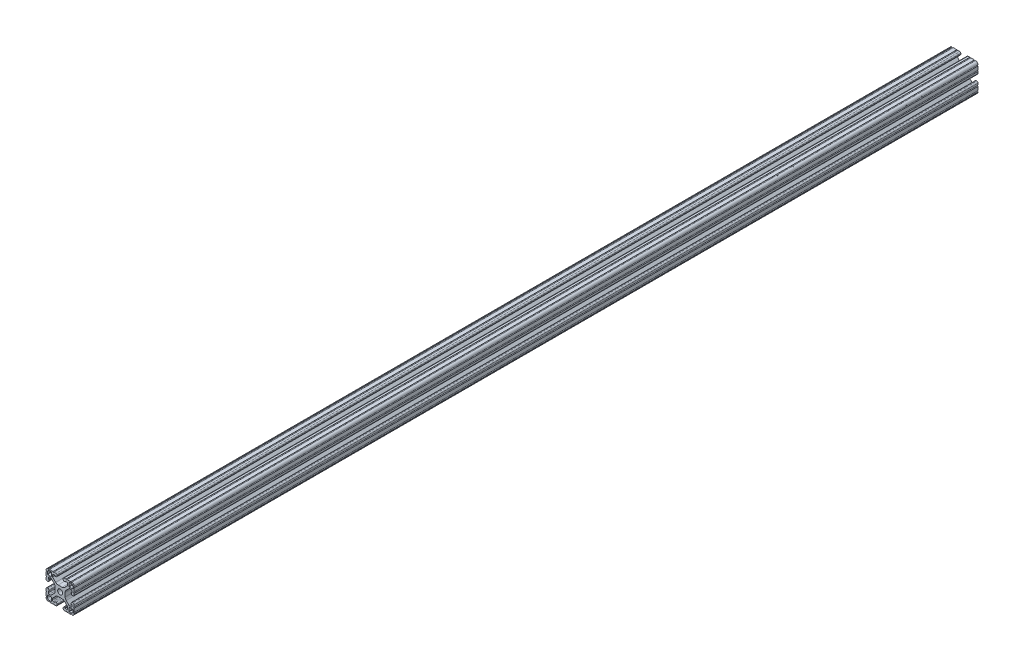
SolidWorks part; units mm, degrees
material "6061 Alloy"
ref_plane "Front Plane" through (0, 0, 0) normal (0, 0, 1) x (1, 0, 0)
ref_plane "Top Plane" through (0, 0, 0) normal (0, 1, 0) x (1, 0, 0)
ref_plane "Right Plane" through (0, 0, 0) normal (1, 0, 0) x (0, 0, -1)
sketch "Sketch1" plane through (0, 0, 0) normal (0, 0, 1) x (1, 0, 0)
  line L0 (0, 21.507) -> (0, -20.9529) construction
  line L1 (20.4424, 0) -> (-20.8151, 0) construction
  line L2 (10.0267, -12.1519) -> (6.0215, -8.1473)
  line L3 (-10.0267, 12.1519) -> (-6.0215, 8.1473)
  line L4 (-10.287, 14.5547) -> (-10.287, 12.7802)
  line L5 (-6.8141, 15.8247) -> (-9.017, 15.8247)
  line L6 (10.287, -14.5547) -> (10.287, -12.7802)
  line L7 (-6.8141, 14.986) -> (-6.8141, 15.8247)
  line L8 (6.8141, -15.8247) -> (9.017, -15.8247)
  line L9 (-2.6631, -6.7564) -> (2.6631, -6.7564)
  line L10 (6.8141, -14.986) -> (6.8141, -15.8247)
  line L11 (5.6388, -14.986) -> (6.8141, -14.986)
  line L12 (4.064, -17.4752) -> (4.064, -16.5608)
  line L13 (7.9756, -19.05) -> (5.6388, -19.05)
  line L14 (14.3256, -19.05) -> (9.4996, -19.05)
  line L15 (15.875, -19.05) -> (15.8496, -19.05)
  line L16 (19.05, -15.8496) -> (19.05, -15.875)
  line L17 (19.05, -9.4996) -> (19.05, -14.3256)
  line L18 (19.05, -5.6388) -> (19.05, -7.9756)
  line L19 (-5.6388, 14.986) -> (-6.8141, 14.986)
  line L20 (-4.064, 17.4752) -> (-4.064, 16.5608)
  line L21 (-7.9756, 19.05) -> (-5.6388, 19.05)
  line L22 (16.5608, -4.064) -> (17.4752, -4.064)
  line L23 (-14.3256, 19.05) -> (-9.4996, 19.05)
  line L24 (14.986, -6.7506) -> (14.986, -5.6388)
  line L25 (15.879, -6.7506) -> (14.986, -6.7506)
  line L26 (-15.875, 19.05) -> (-15.8496, 19.05)
  line L27 (-19.05, 15.8496) -> (-19.05, 15.875)
  line L28 (15.879, -8.9192) -> (15.879, -6.7506)
  line L29 (12.7428, -10.1892) -> (14.609, -10.1892)
  line L30 (-19.05, 9.4996) -> (-19.05, 14.3256)
  line L31 (-19.05, 5.6388) -> (-19.05, 7.9756)
  line L32 (8.1479, -5.9632) -> (12.1142, -9.9289)
  line L33 (16.891, -11.8618) -> (12.2428, -11.8618)
  line L34 (11.8618, -12.2428) -> (11.8618, -16.891)
  line L35 (12.2428, -17.272) -> (14.478, -17.272)
  line L36 (17.272, 14.478) -> (17.272, 12.2428)
  line L37 (12.2428, 17.272) -> (14.478, 17.272)
  line L38 (11.8618, 12.2428) -> (11.8618, 16.891)
  line L39 (16.891, 11.8618) -> (12.2428, 11.8618)
  line L40 (17.272, -14.478) -> (17.272, -12.2428)
  line L41 (-16.5608, 4.064) -> (-17.4752, 4.064)
  line L42 (-14.986, 6.7506) -> (-14.986, 5.6388)
  line L43 (-15.879, 6.7506) -> (-14.986, 6.7506)
  line L44 (-15.879, 8.9192) -> (-15.879, 6.7506)
  line L45 (-12.7428, 10.1892) -> (-14.609, 10.1892)
  line L46 (-8.1479, 5.9632) -> (-12.1142, 9.9289)
  line L47 (-6.7564, -2.6043) -> (-6.7564, 2.6043)
  line L48 (-17.272, -14.478) -> (-17.272, -12.2428)
  line L49 (-16.891, 11.8618) -> (-12.2428, 11.8618)
  line L50 (-11.8618, 12.2428) -> (-11.8618, 16.891)
  line L51 (-12.2428, 17.272) -> (-14.478, 17.272)
  line L52 (-17.272, 14.478) -> (-17.272, 12.2428)
  line L53 (-12.2428, -17.272) -> (-14.478, -17.272)
  line L54 (-11.8618, -12.2428) -> (-11.8618, -16.891)
  line L55 (-16.891, -11.8618) -> (-12.2428, -11.8618)
  line L56 (-8.1479, -5.9632) -> (-12.1142, -9.9289)
  line L57 (-12.7428, -10.1892) -> (-14.609, -10.1892)
  line L58 (-15.879, -8.9192) -> (-15.879, -6.7506)
  line L59 (-15.879, -6.7506) -> (-14.986, -6.7506)
  line L60 (-14.986, -6.7506) -> (-14.986, -5.6388)
  line L61 (-16.5608, -4.064) -> (-17.4752, -4.064)
  line L62 (-19.05, -5.6388) -> (-19.05, -7.9756)
  line L63 (-19.05, -9.4996) -> (-19.05, -14.3256)
  line L64 (-19.05, -15.8496) -> (-19.05, -15.875)
  line L65 (-15.875, -19.05) -> (-15.8496, -19.05)
  line L66 (-14.3256, -19.05) -> (-9.4996, -19.05)
  line L67 (-7.9756, -19.05) -> (-5.6388, -19.05)
  line L68 (-4.064, -17.4752) -> (-4.064, -16.5608)
  line L69 (-5.6388, -14.986) -> (-6.8141, -14.986)
  line L70 (-6.8141, -14.986) -> (-6.8141, -15.8247)
  line L71 (-6.8141, -15.8247) -> (-9.017, -15.8247)
  line L72 (-10.287, -14.5547) -> (-10.287, -12.7802)
  line L73 (-10.0267, -12.1519) -> (-6.0215, -8.1473)
  line L95 (6.7564, -2.6043) -> (6.7564, 2.6043)
  line L96 (8.1479, 5.9632) -> (12.1142, 9.9289)
  line L97 (12.7428, 10.1892) -> (14.609, 10.1892)
  line L98 (15.879, 8.9192) -> (15.879, 6.7506)
  line L99 (15.879, 6.7506) -> (14.986, 6.7506)
  line L100 (14.986, 6.7506) -> (14.986, 5.6388)
  line L101 (16.5608, 4.064) -> (17.4752, 4.064)
  line L102 (19.05, 5.6388) -> (19.05, 7.9756)
  line L103 (19.05, 9.4996) -> (19.05, 14.3256)
  line L104 (19.05, 15.8496) -> (19.05, 15.875)
  line L105 (15.875, 19.05) -> (15.8496, 19.05)
  line L106 (14.3256, 19.05) -> (9.4996, 19.05)
  line L107 (7.9756, 19.05) -> (5.6388, 19.05)
  line L108 (4.064, 17.4752) -> (4.064, 16.5608)
  line L109 (5.6388, 14.986) -> (6.8141, 14.986)
  line L110 (6.8141, 14.986) -> (6.8141, 15.8247)
  line L111 (6.8141, 15.8247) -> (9.017, 15.8247)
  line L112 (10.287, 14.5547) -> (10.287, 12.7802)
  line L113 (10.0267, 12.1519) -> (6.0215, 8.1473)
  line L114 (2.6631, 6.7564) -> (-2.6631, 6.7564)
  arc A0 (10.0267, -12.1519) -> (10.287, -12.7802) centre (9.3985, -12.7802) cw
  arc A1 (10.287, -14.5547) -> (9.017, -15.8247) centre (9.017, -14.5547) cw
  arc A2 (4.064, -16.5608) -> (5.6388, -14.986) centre (5.6388, -16.5608) cw
  arc A3 (-10.0267, 12.1519) -> (-10.287, 12.7802) centre (-9.3985, 12.7802) cw
  arc A4 (-10.287, 14.5547) -> (-9.017, 15.8247) centre (-9.017, 14.5547) cw
  arc A5 (5.6388, -19.05) -> (4.064, -17.4752) centre (5.6388, -17.4752) cw
  arc A6 (7.9756, -19.05) -> (9.4996, -19.05) centre (8.7376, -19.05) cw
  arc A7 (-4.064, 16.5608) -> (-5.6388, 14.986) centre (-5.6388, 16.5608) cw
  arc A8 (14.3256, -19.05) -> (15.8496, -19.05) centre (15.0876, -19.05) cw
  arc A9 (19.05, -15.875) -> (15.875, -19.05) centre (15.875, -15.875) cw
  arc A10 (6.0215, -8.1473) -> (2.6631, -6.7564) centre (2.6631, -11.5062) ccw
  arc A11 (-6.0215, -8.1473) -> (-2.6631, -6.7564) centre (-2.6631, -11.5062) cw
  arc A12 (19.05, -15.8496) -> (19.05, -14.3256) centre (19.05, -15.0876) cw
  arc A13 (19.05, -9.4996) -> (19.05, -7.9756) centre (19.05, -8.7376) cw
  arc A14 (17.4752, -4.064) -> (19.05, -5.6388) centre (17.4752, -5.6388) cw
  arc A15 (14.986, -5.6388) -> (16.5608, -4.064) centre (16.5608, -5.6388) cw
  arc A16 (15.879, -8.9192) -> (14.609, -10.1892) centre (14.609, -8.9192) cw
  arc A17 (12.7428, -10.1892) -> (12.1142, -9.9289) centre (12.7428, -9.3002) cw
  arc A18 (16.891, -11.8618) -> (17.272, -12.2428) centre (16.891, -12.2428) cw
  arc A19 (-5.6388, 19.05) -> (-4.064, 17.4752) centre (-5.6388, 17.4752) cw
  arc A20 (-7.9756, 19.05) -> (-9.4996, 19.05) centre (-8.7376, 19.05) cw
  arc A21 (-14.3256, 19.05) -> (-15.8496, 19.05) centre (-15.0876, 19.05) cw
  arc A22 (11.8618, -12.2428) -> (12.2428, -11.8618) centre (12.2428, -12.2428) cw
  arc A23 (-19.05, 15.875) -> (-15.875, 19.05) centre (-15.875, 15.875) cw
  arc A24 (12.2428, -17.272) -> (11.8618, -16.891) centre (12.2428, -16.891) cw
  arc A25 (17.272, -14.478) -> (14.478, -17.272) centre (14.478, -14.478) cw
  arc A26 (-19.05, 15.8496) -> (-19.05, 14.3256) centre (-19.05, 15.0876) cw
  arc A27 (-19.05, 9.4996) -> (-19.05, 7.9756) centre (-19.05, 8.7376) cw
  arc A28 (-17.4752, 4.064) -> (-19.05, 5.6388) centre (-17.4752, 5.6388) cw
  arc A29 (-14.986, 5.6388) -> (-16.5608, 4.064) centre (-16.5608, 5.6388) cw
  arc A30 (-15.879, 8.9192) -> (-14.609, 10.1892) centre (-14.609, 8.9192) cw
  arc A31 (-12.7428, 10.1892) -> (-12.1142, 9.9289) centre (-12.7428, 9.3002) cw
  arc A32 (-8.1479, 5.9632) -> (-6.7564, 2.6043) centre (-11.5062, 2.6043) cw
  arc A33 (-6.7564, -2.6043) -> (-8.1479, -5.9632) centre (-11.5062, -2.6043) cw
  arc A34 (-16.891, 11.8618) -> (-17.272, 12.2428) centre (-16.891, 12.2428) cw
  arc A35 (-11.8618, 12.2428) -> (-12.2428, 11.8618) centre (-12.2428, 12.2428) cw
  arc A36 (17.272, 14.478) -> (14.478, 17.272) centre (14.478, 14.478) ccw
  arc A37 (12.2428, 17.272) -> (11.8618, 16.891) centre (12.2428, 16.891) ccw
  arc A38 (11.8618, 12.2428) -> (12.2428, 11.8618) centre (12.2428, 12.2428) ccw
  arc A39 (16.891, 11.8618) -> (17.272, 12.2428) centre (16.891, 12.2428) ccw
  arc A40 (-12.2428, 17.272) -> (-11.8618, 16.891) centre (-12.2428, 16.891) cw
  circle A41 centre (0, 0) radius 3.3274
  arc A42 (-17.272, 14.478) -> (-14.478, 17.272) centre (-14.478, 14.478) cw
  arc A43 (-17.272, -14.478) -> (-14.478, -17.272) centre (-14.478, -14.478) ccw
  arc A44 (-12.2428, -17.272) -> (-11.8618, -16.891) centre (-12.2428, -16.891) ccw
  arc A45 (-11.8618, -12.2428) -> (-12.2428, -11.8618) centre (-12.2428, -12.2428) ccw
  arc A46 (-16.891, -11.8618) -> (-17.272, -12.2428) centre (-16.891, -12.2428) ccw
  arc A47 (-12.7428, -10.1892) -> (-12.1142, -9.9289) centre (-12.7428, -9.3002) ccw
  arc A48 (-15.879, -8.9192) -> (-14.609, -10.1892) centre (-14.609, -8.9192) ccw
  arc A49 (-14.986, -5.6388) -> (-16.5608, -4.064) centre (-16.5608, -5.6388) ccw
  arc A50 (-17.4752, -4.064) -> (-19.05, -5.6388) centre (-17.4752, -5.6388) ccw
  arc A51 (-19.05, -9.4996) -> (-19.05, -7.9756) centre (-19.05, -8.7376) ccw
  arc A52 (-19.05, -15.8496) -> (-19.05, -14.3256) centre (-19.05, -15.0876) ccw
  arc A53 (-19.05, -15.875) -> (-15.875, -19.05) centre (-15.875, -15.875) ccw
  arc A54 (-14.3256, -19.05) -> (-15.8496, -19.05) centre (-15.0876, -19.05) ccw
  arc A55 (-7.9756, -19.05) -> (-9.4996, -19.05) centre (-8.7376, -19.05) ccw
  arc A56 (-5.6388, -19.05) -> (-4.064, -17.4752) centre (-5.6388, -17.4752) ccw
  arc A57 (-4.064, -16.5608) -> (-5.6388, -14.986) centre (-5.6388, -16.5608) ccw
  arc A58 (-10.287, -14.5547) -> (-9.017, -15.8247) centre (-9.017, -14.5547) ccw
  arc A59 (-10.0267, -12.1519) -> (-10.287, -12.7802) centre (-9.3985, -12.7802) ccw
  arc A86 (6.7564, -2.6043) -> (8.1479, -5.9632) centre (11.5062, -2.6043) ccw
  arc A87 (8.1479, 5.9632) -> (6.7564, 2.6043) centre (11.5062, 2.6043) ccw
  arc A88 (12.7428, 10.1892) -> (12.1142, 9.9289) centre (12.7428, 9.3002) ccw
  arc A89 (15.879, 8.9192) -> (14.609, 10.1892) centre (14.609, 8.9192) ccw
  arc A90 (14.986, 5.6388) -> (16.5608, 4.064) centre (16.5608, 5.6388) ccw
  arc A91 (17.4752, 4.064) -> (19.05, 5.6388) centre (17.4752, 5.6388) ccw
  arc A92 (19.05, 9.4996) -> (19.05, 7.9756) centre (19.05, 8.7376) ccw
  arc A93 (19.05, 15.8496) -> (19.05, 14.3256) centre (19.05, 15.0876) ccw
  arc A94 (19.05, 15.875) -> (15.875, 19.05) centre (15.875, 15.875) ccw
  arc A95 (14.3256, 19.05) -> (15.8496, 19.05) centre (15.0876, 19.05) ccw
  arc A96 (7.9756, 19.05) -> (9.4996, 19.05) centre (8.7376, 19.05) ccw
  arc A97 (5.6388, 19.05) -> (4.064, 17.4752) centre (5.6388, 17.4752) ccw
  arc A98 (4.064, 16.5608) -> (5.6388, 14.986) centre (5.6388, 16.5608) ccw
  arc A99 (10.287, 14.5547) -> (9.017, 15.8247) centre (9.017, 14.5547) ccw
  arc A100 (10.0267, 12.1519) -> (10.287, 12.7802) centre (9.3985, 12.7802) ccw
  arc A101 (2.6631, 6.7564) -> (6.0215, 8.1473) centre (2.6631, 11.5062) ccw
  arc A102 (-6.0215, 8.1473) -> (-2.6631, 6.7564) centre (-2.6631, 11.5062) ccw
  dimension "D1" = 6.6548
  dimension "D2" = 38.1
  dimension "D3" = 20.574
  dimension "D4" = 12.2936
  dimension "D5" = 19.05
  dimension "D6" = 8.128
  dimension "D7" = 3.048
  dimension "D8" = 4.064
  dimension "D9" = 13.5128
extrude "Extrude1" add sketch "Sketch1" against normal blind 1219.2
